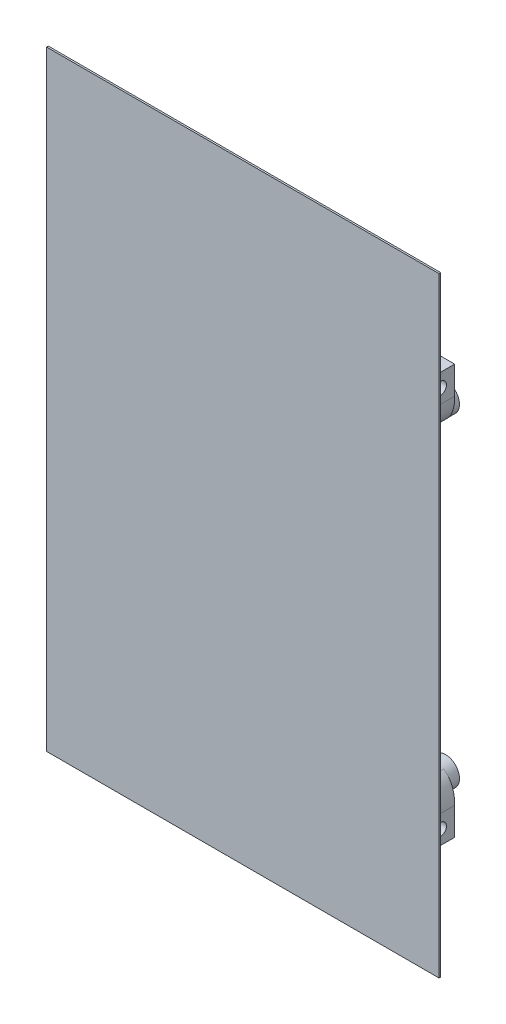
SolidWorks part; units mm, degrees
ref_plane "Front Plane" through (0, 0, 0) normal (0, 0, 1) x (1, 0, 0)
ref_plane "Top Plane" through (0, 0, 0) normal (0, 1, 0) x (1, 0, 0)
ref_plane "Right Plane" through (0, 0, 0) normal (1, 0, 0) x (0, 0, -1)
sketch "Sketch1" plane through (0, 0, 0) normal (0, 0, 1) x (1, 0, 0)
  line L1 (109, 161.3091) -> (-4, 161.3091)
  line L2 (109, 161.3091) -> (109, -14.3091)
  line L3 (109, -14.3091) -> (-4, -14.3091)
  line L4 (-4, 161.3091) -> (-4, -14.3091)
extrude "Boss-Extrude1" add sketch "Sketch1" along normal blind 0.5
sketch "Sketch2" plane through (0, 0, 0) normal (0, 0, -1) x (-1, 0, 0)
  circle A0 centre (-5.6, 26.85) radius 2 construction
  circle A1 centre (-99.4, 26.85) radius 2 construction
  circle A2 centre (-99.4, 120.15) radius 2 construction
  circle A3 centre (-5.6, 120.15) radius 2 construction
  circle A4 centre (-5.6, 26.85) radius 2
  circle A5 centre (-99.4, 26.85) radius 2
  circle A6 centre (-99.4, 120.15) radius 2
  circle A7 centre (-5.6, 120.15) radius 2
  circle A8 centre (-5.6, 120.15) radius 4
  circle A9 centre (-5.6, 26.85) radius 4
  circle A10 centre (-99.4, 26.85) radius 4
  circle A11 centre (-99.4, 120.15) radius 4
  dimension "D1" = 8
extrude "Boss-Extrude2" add sketch "Sketch2" along normal up to surface (11 mm away)
sketch "Sketch3" plane through (0, 0, 0) normal (0, 0, -1) x (-1, 0, 0)
  line L0 (-99.4, 120.15) -> (-5.6, 120.15) construction
  line L1 (-7.3321, 123.15) -> (-8.2458, 123.15)
  line L2 (-9.0641, 120.15) -> (-7.3321, 117.15)
  line L3 (-7.3321, 117.15) -> (-3.8679, 117.15)
  line L4 (-3.8679, 117.15) -> (-2.1359, 120.15)
  line L5 (-2.1359, 120.15) -> (-3.8679, 123.15)
  line L6 (-3.8679, 123.15) -> (-7.3321, 123.15)
  line L7 (-7.3321, 123.15) -> (-9.0641, 120.15)
  line L8 (-7.3321, 117.15) -> (-8.2458, 117.15)
  line L9 (-52.5, 161.3091) -> (-52.5, -14.3091) construction
  line L10 (-109, 161.3091) -> (4, 161.3091) construction
  line L11 (4, -14.3091) -> (-109, -14.3091) construction
  line L12 (-97.6679, 117.15) -> (-96.7542, 117.15)
  line L13 (-97.6679, 123.15) -> (-95.9359, 120.15)
  line L14 (-95.9359, 120.15) -> (-97.6679, 117.15)
  line L15 (-97.6679, 117.15) -> (-101.1321, 117.15)
  line L16 (-101.1321, 117.15) -> (-102.8641, 120.15)
  line L17 (-102.8641, 120.15) -> (-101.1321, 123.15)
  line L18 (-101.1321, 123.15) -> (-97.6679, 123.15)
  line L19 (-97.6679, 123.15) -> (-96.7542, 123.15)
  line L20 (-109, 73.5) -> (4, 73.5) construction
  line L21 (-109, -14.3091) -> (-109, 161.3091) construction
  line L22 (4, 161.3091) -> (4, -14.3091) construction
  line L23 (-7.3321, 29.85) -> (-8.2458, 29.85)
  line L24 (-7.3321, 29.85) -> (-3.8679, 29.85)
  line L25 (-9.0641, 26.85) -> (-7.3321, 29.85)
  line L26 (-2.1359, 26.85) -> (-3.8679, 23.85)
  line L27 (-3.8679, 29.85) -> (-2.1359, 26.85)
  line L28 (-7.3321, 23.85) -> (-9.0641, 26.85)
  line L29 (-3.8679, 23.85) -> (-7.3321, 23.85)
  line L30 (-7.3321, 23.85) -> (-8.2458, 23.85)
  line L31 (-97.6679, 23.85) -> (-96.7542, 23.85)
  line L32 (-101.1321, 23.85) -> (-97.6679, 23.85)
  line L33 (-102.8641, 26.85) -> (-101.1321, 23.85)
  line L34 (-101.1321, 29.85) -> (-102.8641, 26.85)
  line L35 (-97.6679, 29.85) -> (-101.1321, 29.85)
  line L36 (-95.9359, 26.85) -> (-97.6679, 29.85)
  line L37 (-97.6679, 23.85) -> (-95.9359, 26.85)
  line L38 (-97.6679, 29.85) -> (-96.7542, 29.85)
  circle A0 centre (-5.6, 120.15) radius 3 construction
  circle A1 centre (-5.6, 120.15) radius 4 construction
  circle A2 centre (-5.6, 120.15) radius 4 construction
  circle M15 centre (-99.4, 120.15) radius 4
  circle M16 centre (-99.4, 26.85) radius 4
  circle M17 centre (-5.6, 26.85) radius 4
  circle M18 centre (-5.6, 120.15) radius 4
  dimension "D1" = 6
extrude "Cut-Extrude1" cut sketch "Sketch3" along normal blind 3 contours L18 L17 L16 L15 L14 L13 | L19 L13 L14 L12 M15 | L6 L7 L2 L3 L4 L5 | L8 L2 L7 L1 M18 | L29 L26 L27 L24 L25 L28 | L30 L28 L25 L23 M17 | L32 L37 L36 L35 L34 L33 | L38 L36 L37 L31 M16
sketch "Sketch4" plane through (0, 0, 0) normal (0, 0, -1) x (-1, 0, 0)
  line L0 (-105, -14.3091) -> (-105, 12.5) construction
  line L1 (-105, 14.5) -> (-100, 14.5)
  line L2 (-105, 14.5) -> (-105, 22.5)
  line L3 (-105, 22.5) -> (-100, 22.5)
  line L4 (-100, 14.5) -> (-100, 22.5)
  line L5 (-100, 18.5) -> (-105, 18.5) construction
  line L7 (-104.2951, 26.85) -> (-99.4, 26.85) construction
  line L8 (-100, 22.5) -> (-100, 22.8953)
  line L15 (-109, 18.5) -> (-105, 18.5) construction
  arc A0 (-96.7542, 29.85) -> (-96.7542, 23.85) centre (-99.4, 26.85) ccw construction
  circle A1 centre (-99.4, 26.85) radius 4 construction
  spline S1 degree 3 poles (-105, 22.5) (-105, 25.5429) (-104.3608, 28.0669) (-101.8496, 30.0122) knots 0 0 0 0 1 1 1 1
  point P8 (-100, 23.3244)
  point P26 (-100, 21.1429)
  point P27 (0, 0)
  point P28 (-99.2, 17.1247)
  arc M10 (-96.7542, 23.85) -> (-96.7542, 29.85) centre (-99.4, 26.85) cw
  dimension "D1" = 8
  dimension "D2" = 5
extrude "Boss-Extrude3" add sketch "Sketch4" along normal blind 8 contours L1 L4 L3 L2 | S1 L3 L8 M10
sketch "Sketch5" plane through (100, 0, 0) normal (-1, 0, 0) x (0, 0, 1)
  circle A1 centre (-3.8964, 18.5) radius 1.75
  circle A2 centre (-3.8964, 18.5) radius 2.9 construction
  dimension "D1" = 3.5
extrude "Cut-Extrude2" cut sketch "Sketch5" against normal up to next
sketch "Sketch6" plane through (100, 0, 0) normal (-1, 0, 0) x (0, 0, 1)
  line L1 (-3.8964, 21.9641) -> (-6.8964, 20.2321)
  line L2 (-6.8964, 20.2321) -> (-6.8964, 16.7679)
  line L3 (-6.8964, 16.7679) -> (-3.8964, 15.0359)
  line L4 (-3.8964, 15.0359) -> (-0.8964, 16.7679)
  line L5 (-0.8964, 16.7679) -> (-0.8964, 20.2321)
  line L6 (-0.8964, 20.2321) -> (-3.8964, 21.9641)
  circle A0 centre (-3.8964, 18.5) radius 3 construction
  dimension "D1" = 6
extrude "Cut-Extrude3" cut sketch "Sketch6" against normal blind 2.5
ref_plane "Plane1" through (0, 73.5, 0) normal (0, -1, 0) x (-1, 0, 0)
ref_plane "Plane2" through (52.5, 0, 0) normal (-1, 0, 0) x (0, 0, 1)
mirror "Mirror1" about plane through (52.5, 0, 0) normal (-1, 0, 0) of "Cut-Extrude3", "Cut-Extrude2", "Boss-Extrude3"
mirror "Mirror2" about plane through (0, 73.5, 0) normal (0, -1, 0) of "Cut-Extrude3", "Cut-Extrude2", "Boss-Extrude3", "Mirror1"
